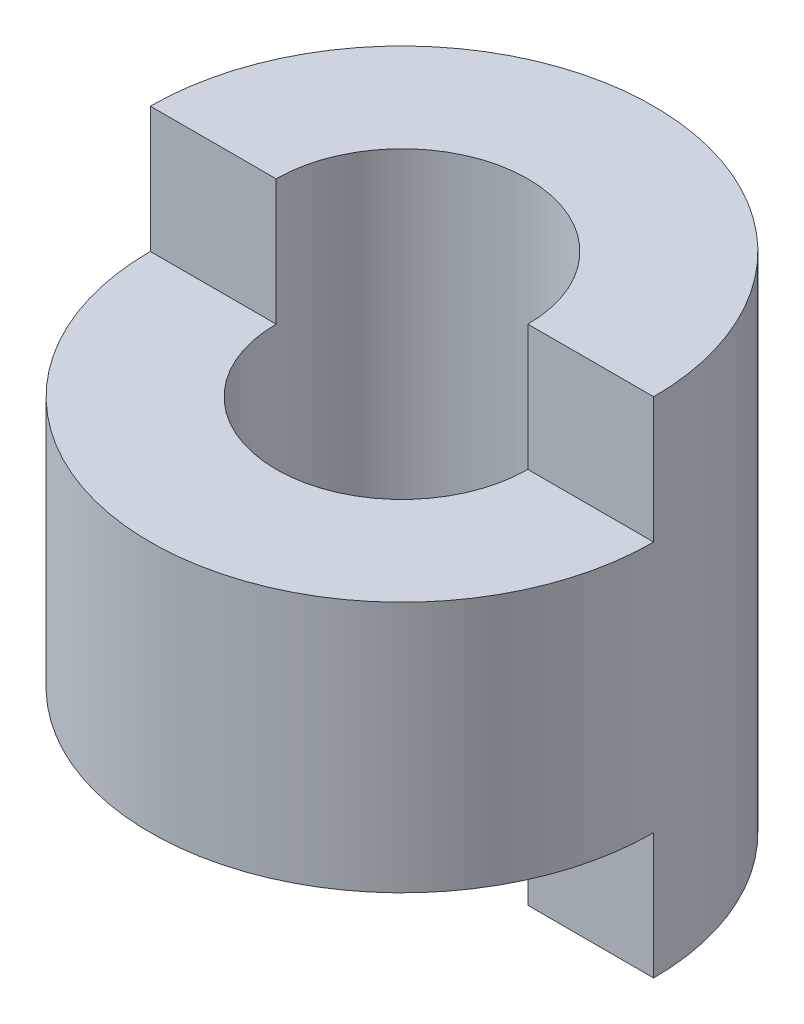
SolidWorks part; units mm, degrees
ref_plane "Front Plane" through (0, 0, 0) normal (0, 0, 1) x (1, 0, 0)
ref_plane "Top Plane" through (0, 0, 0) normal (0, 1, 0) x (1, 0, 0)
ref_plane "Right Plane" through (0, 0, 0) normal (1, 0, 0) x (0, 0, -1)
sketch "Sketch1" plane through (0, 0, 0) normal (0, 0, 1) x (1, 0, 0)
  line L1 (0, 0) -> (10, 0)
  line L2 (0, 0) -> (0, 20)
  line L3 (0, 20) -> (10, 20)
  line L4 (10, 0) -> (10, 20)
  dimension "D1" = 20
  dimension "D2" = 10
revolve "Revolve1" add sketch "Sketch1" angle 360 about L2
sketch "Sketch2" plane through (0, 20, 0) normal (0, 1, 0) x (1, 0, 0)
  circle A0 centre (0, 0) radius 5
  dimension "D1" = 10
extrude "Cut-Extrude1" cut sketch "Sketch2" against normal blind 20
sketch "Sketch3" plane through (0, 20, 0) normal (0, 1, 0) x (1, 0, 0)
  line L0 (-10, 0) -> (-5, 0)
  line L1 (5, 0) -> (10, 0)
  arc A0 (-10, 0) -> (10, 0) centre (0, 0) ccw
  circle A1 centre (0, 0) radius 10 construction
  arc A2 (-5, 0) -> (5, 0) centre (0, 0) ccw
  circle A3 centre (0, 0) radius 5 construction
  dimension "D3" = 5
  dimension "D4" = 10
  dimension "D1" = 5
  dimension "D2" = 5
extrude "Cut-Extrude2" cut sketch "Sketch3" against normal blind 5
sketch "Sketch4" plane through (0, 0, 0) normal (0, -1, 0) x (1, 0, 0)
  line L0 (-10, 0) -> (-5, 0)
  line L1 (5, 0) -> (10, 0)
  arc A0 (-10, 0) -> (10, 0) centre (0, 0) cw
  arc A1 (-5, 0) -> (5, 0) centre (0, 0) cw
  circle A2 centre (0, 0) radius 5 construction
extrude "Cut-Extrude4" cut sketch "Sketch4" against normal blind 5
